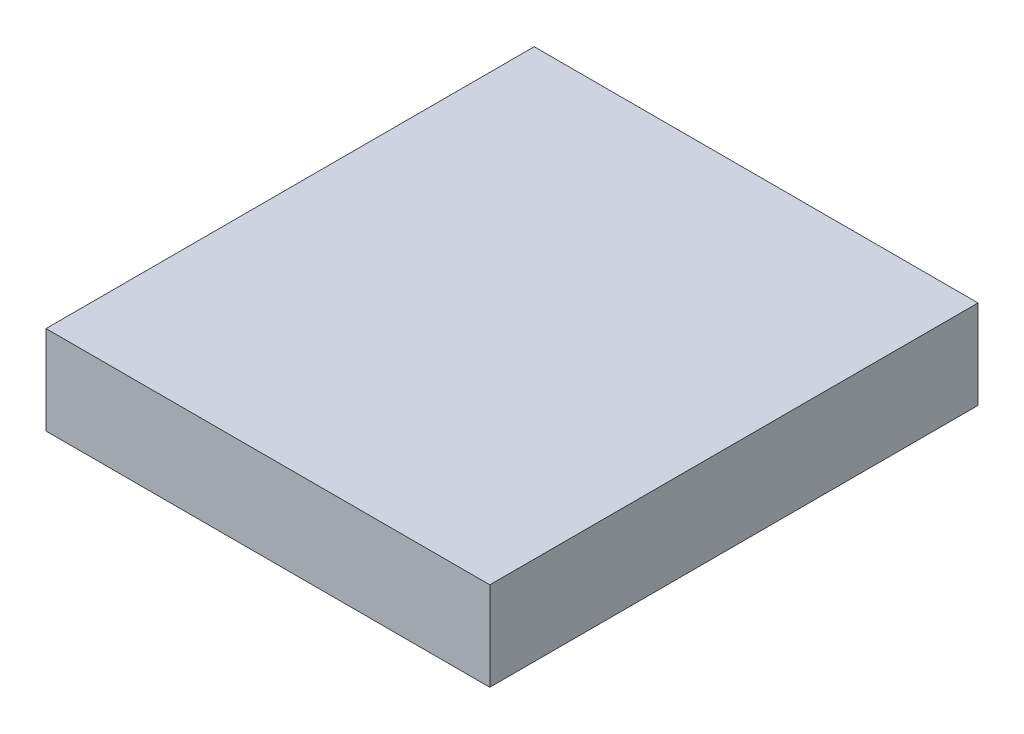
SolidWorks part; units mm, degrees
ref_plane "Front Plane" through (0, 0, 0) normal (0, 0, 1) x (1, 0, 0)
ref_plane "Top Plane" through (0, 0, 0) normal (0, 1, 0) x (1, 0, 0)
ref_plane "Right Plane" through (0, 0, 0) normal (1, 0, 0) x (0, 0, -1)
sketch "Sketch1" plane through (0, 0, 0) normal (0, 1, 0) x (1, 0, 0)
  line L1 (-12.5, -13.75) -> (12.5, -13.75)
  line L2 (-12.5, -13.75) -> (-12.5, 13.75)
  line L3 (-12.5, 13.75) -> (12.5, 13.75)
  line L4 (12.5, -13.75) -> (12.5, 13.75)
  line L5 (-12.5, -13.75) -> (12.5, 13.75) construction
  line L6 (-12.5, 13.75) -> (12.5, -13.75) construction
  point P0 (0, 0)
  dimension "D1" = 27.5
  dimension "D2" = 25
extrude "Boss-Extrude4" add sketch "Sketch1" along normal blind 5
